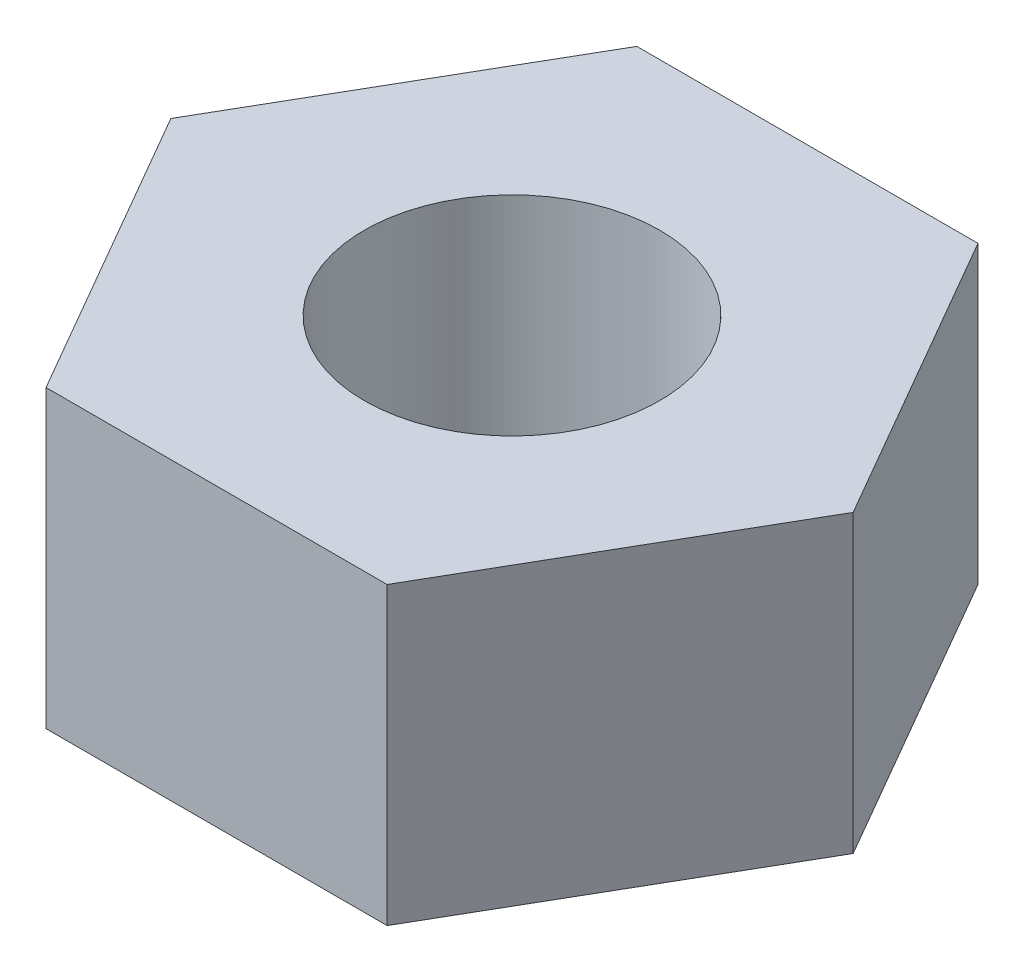
SolidWorks part; units mm, degrees
ref_plane "Front Plane" through (0, 0, 0) normal (0, 0, 1) x (1, 0, 0)
ref_plane "Top Plane" through (0, 0, 0) normal (0, 1, 0) x (1, 0, 0)
ref_plane "Right Plane" through (0, 0, 0) normal (1, 0, 0) x (0, 0, -1)
sketch "Sketch1" plane through (0, 0, 0) normal (0, 1, 0) x (1, 0, 0)
  line L1 (11.547, 0) -> (5.7735, 10)
  line L2 (5.7735, 10) -> (-5.7735, 10)
  line L3 (-5.7735, 10) -> (-11.547, 0)
  line L4 (-11.547, 0) -> (-5.7735, -10)
  line L5 (-5.7735, -10) -> (5.7735, -10)
  line L6 (5.7735, -10) -> (11.547, 0)
  circle A1 centre (0, 0) radius 5
  circle A2 centre (0, 0) radius 10 construction
  dimension "D1" = 20
  dimension "D2" = 10
extrude "Boss-Extrude1" add sketch "Sketch1" along normal blind 10
